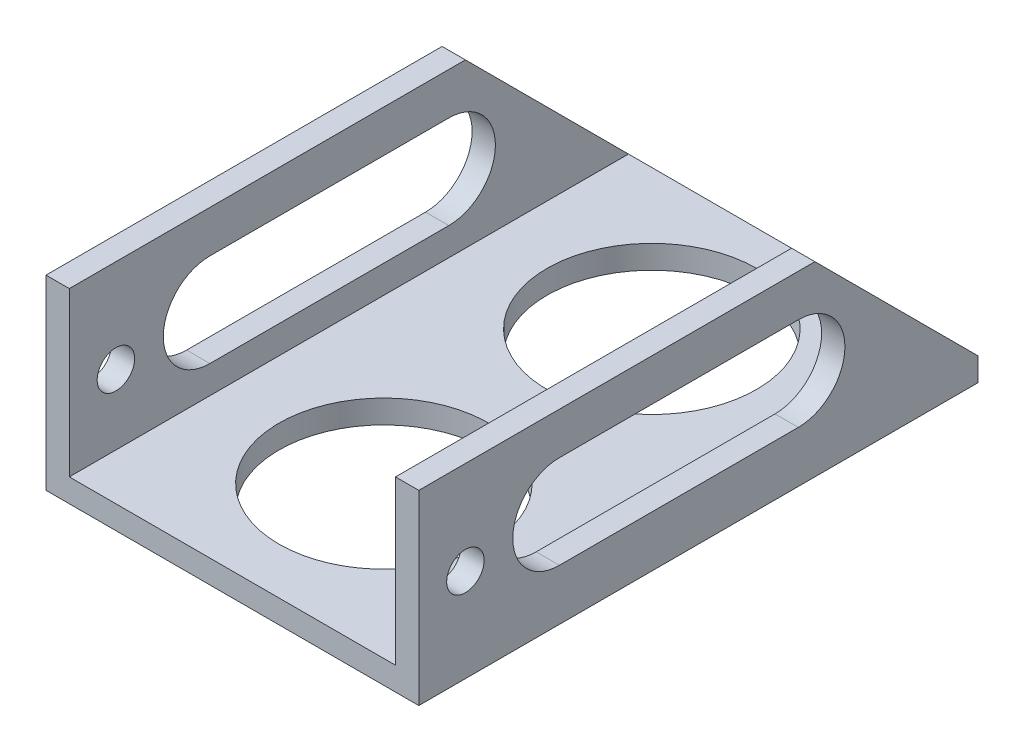
SolidWorks part; units mm, degrees
material "6063-T6"
ref_plane "Front" through (0, 0, 0) normal (0, 0, 1) x (1, 0, 0)
ref_plane "Top" through (0, 0, 0) normal (0, 1, 0) x (1, 0, 0)
ref_plane "Right" through (0, 0, 0) normal (1, 0, 0) x (0, 0, -1)
sketch "Sketch1" plane through (0, 0, 0) normal (0, 0, 1) x (1, 0, 0)
  line L0 (3.175, 3.175) -> (3.175, 25.4)
  line L1 (0, 0) -> (50.8, 0)
  line L2 (0, 0) -> (0, 25.4)
  line L4 (50.8, 0) -> (50.8, 25.4)
  line L5 (3.175, 3.175) -> (47.625, 3.175)
  line L6 (47.625, 3.175) -> (47.625, 25.4)
  line L7 (0, 25.4) -> (3.175, 25.4)
  line L8 (50.8, 25.4) -> (47.625, 25.4)
  dimension "D1" = 25.4
  dimension "D2" = 50.8
  dimension "D3" = 3.175
extrude "Boss-Extrude1" add sketch "Sketch1" along normal blind 76.2
sketch "Sketch2" plane through (0, 0, 0) normal (0, -1, 0) x (1, 0, 0)
  line L0 (0, 0) -> (50.8, 0) construction
  circle A0 centre (25.4, 19.05) radius 14.2875
  dimension "D1" = 28.575
  dimension "D2" = 19.05
extrude "Cut-Extrude1" cut sketch "Sketch2" against normal up to next
sketch "Sketch3" plane through (0, 0, 0) normal (-1, 0, 0) x (0, 0, 1)
  circle A0 centre (69.85, 12.7) radius 2.5527 construction
  circle A1 centre (69.85, 12.7) radius 2.5527
extrude "Cut-Extrude2" cut sketch "Sketch3" against normal through all
sketch "Sketch4" plane through (47.625, 0, 0) normal (-1, 0, 0) x (0, 0, 1)
  line L0 (0, 3.175) -> (22.225, 25.4)
  line L1 (76.2, 25.4) -> (0, 25.4) construction
  line L2 (22.225, 25.4) -> (0, 25.4)
  line L3 (0, 25.4) -> (0, 3.175)
  dimension "D1" = 45
extrude "Cut-Extrude3" cut sketch "Sketch4" against normal through all and the other way through all
sketch "Sketch5" plane through (0, 3.175, 0) normal (0, 1, 0) x (1, 0, 0)
  line L0 (25.4, -69.85) -> (25.4, -76.2) construction
  line L1 (47.625, -76.2) -> (3.175, -76.2) construction
  circle A0 centre (25.4, -55.5625) radius 14.2875
  dimension "D1" = 28.575
  dimension "D2" = 6.35
extrude "Cut-Extrude4" cut sketch "Sketch5" against normal up to next
sketch "Sketch6" plane through (47.625, 0, 0) normal (-1, 0, 0) x (0, 0, 1)
  line L0 (24.4859, 13.3238) -> (57.0401, 13.3238) construction
  line L1 (24.4859, 19.6738) -> (57.0401, 19.6738)
  line L2 (24.4859, 6.9738) -> (57.0401, 6.9738)
  arc A0 (24.4859, 19.6738) -> (24.4859, 6.9738) centre (24.4859, 13.3238) ccw
  arc A1 (57.0401, 6.9738) -> (57.0401, 19.6738) centre (57.0401, 13.3238) ccw
  point P2 (40.763, 13.3238)
extrude "Cut-Extrude5" cut sketch "Sketch6" against normal through all and the other way through all
